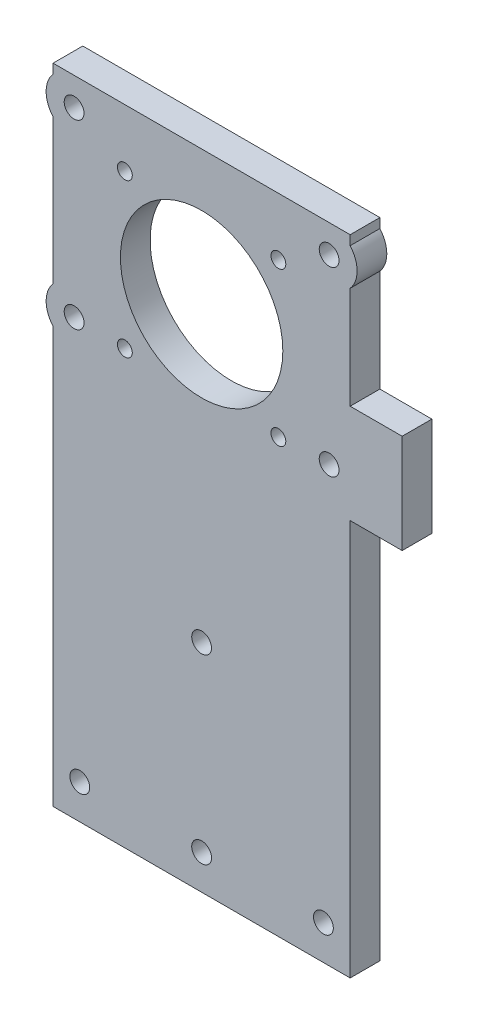
SolidWorks part; units mm, degrees
material "Birch plywood FK"
ref_plane "Спереди" through (0, 0, 0) normal (0, 0, 1) x (1, 0, 0)
ref_plane "Сверху" through (0, 0, 0) normal (0, 1, 0) x (1, 0, 0)
ref_plane "Справа" through (0, 0, 0) normal (1, 0, 0) x (0, 0, -1)
sketch "Эскиз1" plane through (0, 0, 0) normal (0, 0, 1) x (1, 0, 0)
  line L1 (30, -62) -> (-30, -62)
  line L2 (30, -62) -> (30, 62)
  line L3 (30, 62) -> (-30, 62)
  line L4 (-30, -62) -> (-30, 62)
  line L5 (30, -62) -> (-30, 62) construction
  line L6 (30, 62) -> (-30, -62) construction
  point P0 (0, 0)
  dimension "D1" = 60
  dimension "D2" = 124
extrude "Бобышка-Вытянуть1" add sketch "Эскиз1" along normal blind 6
sketch "Эскиз2" plane through (0, 0, 6) normal (0, 0, 1) x (1, 0, 0)
  circle A0 centre (0, 40.85) radius 16.4
  circle A1 centre (-15.5, 56.35) radius 1.5
  circle A2 centre (15.5, 56.35) radius 1.5
  circle A3 centre (15.5, 25.35) radius 1.5
  circle A4 centre (-15.5, 25.35) radius 1.5
  circle A5 centre (0, 40.85) radius 16.4 construction
  dimension "D1" = 3
extrude "Вырез-Вытянуть1" cut sketch "Эскиз2" against normal through all
sketch "Эскиз4" plane through (0, 0, 6) normal (0, 0, 1) x (1, 0, 0)
  circle A0 centre (-24.6, -55) radius 2
  circle A1 centre (0, -55) radius 2
  circle A2 centre (24.6, -55) radius 2
  circle A3 centre (24.6, -55) radius 2 construction
extrude "Вырез-Вытянуть2" cut sketch "Эскиз4" against normal through all
sketch "Эскиз5" plane through (0, 62, 0) normal (0, 1, 0) x (1, 0, 0)
  line L1 (30, -6) -> (-30, -6)
  line L2 (30, -6) -> (30, 0)
  line L3 (30, 0) -> (-30, 0)
  line L4 (-30, -6) -> (-30, 0)
extrude "Бобышка-Вытянуть2" add sketch "Эскиз5" along normal blind 6
sketch "Эскиз6" plane through (0, 0, 0) normal (0, 0, -1) x (-1, 0, 0)
  circle A0 centre (-25.75, 62.35) radius 2
  circle A1 centre (25.75, 62.35) radius 2
  circle A2 centre (25.75, 25.7) radius 2
  circle A3 centre (-25.75, 25.7) radius 2
  circle A4 centre (0, -18.3) radius 2
  circle A5 centre (-25.75, 25.7) radius 2 construction
extrude "Вырез-Вытянуть3" cut sketch "Эскиз6" against normal through all
sketch "Эскиз7" plane through (0, 0, 0) normal (0, 0, -1) x (-1, 0, 0)
  line L0 (-30, 68) -> (30, 68) construction
  line L1 (-30, -62) -> (-30, 68) construction
  line L2 (-40.5, 38) -> (-30, 38)
  line L3 (-40.5, 38) -> (-40.5, 18)
  line L4 (-40.5, 18) -> (-30, 18)
  line L5 (-30, 38) -> (-30, 18)
  line L6 (-40.5, 18) -> (-20.5, 18) construction
  circle A0 centre (-25.75, 62.35) radius 5.65
  circle A1 centre (25.75, 62.35) radius 5.65
  circle A2 centre (25.75, 25.7) radius 5.65
  circle A3 centre (-25.75, 62.35) radius 2
  circle A4 centre (25.75, 62.35) radius 2
  circle A5 centre (25.75, 25.7) radius 2
  circle A6 centre (-25.75, 62.35) radius 2 construction
extrude "Бобышка-Вытянуть3" add sketch "Эскиз7" against normal up to surface (6 mm away) up to face at (-2, -18.3, 6)
